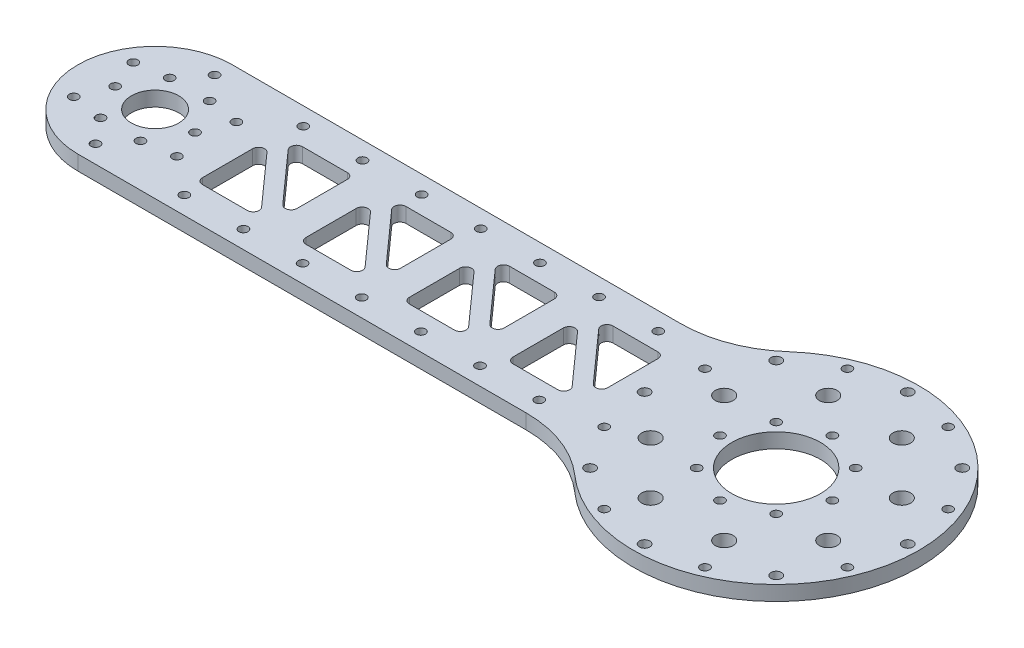
SolidWorks part; units mm, degrees
material "Thornel Mat VMA"
ref_plane "前视基准面" through (0, 0, 0) normal (0, 0, 1) x (1, 0, 0)
ref_plane "上视基准面" through (0, 0, 0) normal (0, 1, 0) x (1, 0, 0)
ref_plane "右视基准面" through (0, 0, 0) normal (1, 0, 0) x (0, 0, -1)
other "Configuration Table"
sketch "草图1" plane through (0, 0, 0) normal (0, 1, 0) x (1, 0, 0)
  line L1 (-105, -26.125) -> (105, -26.125)
  line L2 (-105, -26.125) -> (-105, 26.125)
  line L3 (-105, 26.125) -> (105, 26.125)
  line L4 (105, -26.125) -> (105, 26.125)
  line L5 (-105, -26.125) -> (105, 26.125) construction
  line L6 (-105, 26.125) -> (105, -26.125) construction
  circle A0 centre (-105, 0) radius 26.125
  point P0 (0, 0)
  dimension "D1" = 52.25
  dimension "D2" = 210
extrude "凸台-拉伸1" add sketch "草图1" along normal blind 5 contours A0 L1 L4 L3 | L2 A0 | L2 A0
sketch "草图2" plane through (0, 5, 0) normal (0, 1, 0) x (1, 0, 0)
  circle A0 centre (-105, 0) radius 13.5 construction
  circle A1 centre (-91.5, 0) radius 1.525
  circle A2 centre (-98.25, -11.6913) radius 1.525
  circle A3 centre (-111.75, -11.6913) radius 1.525
  circle A4 centre (-118.5, 0) radius 1.525
  circle A5 centre (-111.75, 11.6913) radius 1.525
  circle A6 centre (-98.25, 11.6913) radius 1.525
  point P17 (-105, 0)
  dimension "D1" = 27
  dimension "D2" = 3.05
  dimension "D3" = 6
extrude "切除-拉伸1" cut sketch "草图2" against normal through all
sketch "草图3" plane through (0, 5, 0) normal (0, 1, 0) x (1, 0, 0)
  line L0 (105, -26.125) -> (105, 26.125) construction
  circle A0 centre (105, 0) radius 48.25
  dimension "D1" = 96.5
extrude "凸台-拉伸2" add sketch "草图3" against normal up to surface (5 mm away) up to face at (-91.5, 0, 1.525)
sketch "草图4" plane through (0, 5, 0) normal (0, 1, 0) x (1, 0, 0)
  line L0 (-105, 26.125) -> (64.4347, 26.125) construction
  line L1 (-47, 26.125) -> (-147, 26.125)
  line L2 (-47, 26.125) -> (-47, -73.875)
  line L3 (-47, -73.875) -> (-147, -73.875)
  line L4 (-147, 26.125) -> (-147, -73.875)
  arc A0 (-105, 26.125) -> (-105, -26.125) centre (-105, 0) ccw construction
  dimension "D1" = 58
  dimension "D2" = 100
  dimension "D3" = 100
sketch "草图6" plane through (0, 5, 0) normal (0, 1, 0) x (1, 0, 0)
  line L0 (118.435, 13.435) -> (105, 0) construction
  line L1 (105, 0) -> (124, 0) construction
  circle A0 centre (105, 0) radius 19 construction
  circle A1 centre (118.435, 13.435) radius 1.525
  circle A2 centre (124, 0) radius 1.525
  circle A3 centre (118.435, -13.435) radius 1.525
  circle A4 centre (105, -19) radius 1.525
  circle A5 centre (91.565, -13.435) radius 1.525
  circle A6 centre (86, 0) radius 1.525
  circle A7 centre (91.565, 13.435) radius 1.525
  circle A8 centre (105, 19) radius 1.525
  point P22 (105, 0)
  dimension "D1" = 38
  dimension "D3" = 3.05
  dimension "D2" = 45
  dimension "D4" = 8
extrude "切除-拉伸4" cut sketch "草图6" against normal through all
sketch "草图7" plane through (0, 5, 0) normal (0, 1, 0) x (1, 0, 0)
  circle A0 centre (105, 0) radius 44.5 construction
  circle A1 centre (149.5, 0) radius 1.775
  circle A3 centre (136.4663, -31.4663) radius 1.775
  circle A4 centre (105, -44.5) radius 1.775
  circle A5 centre (73.5337, -31.4663) radius 1.775
  circle A6 centre (60.5, 0) radius 1.775
  circle A7 centre (73.5337, 31.4663) radius 1.775
  circle A8 centre (105, 44.5) radius 1.775
  circle A9 centre (136.4663, 31.4663) radius 1.775
  point P25 (105, 0)
  dimension "D1" = 89
  dimension "D2" = 3.55
  dimension "D3" = 8
extrude "切除-拉伸5" cut sketch "草图7" against normal through all
fillet "圆角1" radius 40 2 edges at (64.4347, 2.5, 26.125) (64.4347, 2.5, -26.125)
sketch "草图9" plane through (0, 5, 0) normal (0, 1, 0) x (1, 0, 0)
  circle A0 centre (105, 0) radius 14
  dimension "D1" = 28
extrude "切除-拉伸7" cut sketch "草图9" against normal through all
sketch "草图10" plane through (0, 5, 0) normal (0, 1, 0) x (1, 0, 0)
  circle A0 centre (-105, 0) radius 8
  dimension "D1" = 16
extrude "切除-拉伸8" cut sketch "草图10" against normal through all
sketch "草图11" plane through (0, 5, 0) normal (0, 1, 0) x (1, 0, 0)
  circle A0 centre (105, 0) radius 15
  dimension "D1" = 30
extrude "切除-拉伸9" cut sketch "草图11" against normal through all
sketch "草图12" plane through (0, 5, 0) normal (0, 1, 0) x (1, 0, 0)
  line L0 (105, 44.5) -> (105, 0) construction
  line L1 (117.4372, 30.0261) -> (105, 0) construction
  circle A0 centre (105, 0) radius 32.5 construction
  circle A1 centre (117.4372, 30.0261) radius 3
  circle A2 centre (135.0261, 12.4372) radius 3
  circle A3 centre (135.0261, -12.4372) radius 3
  circle A4 centre (117.4372, -30.0261) radius 3
  circle A5 centre (92.5628, -30.0261) radius 3
  circle A6 centre (74.9739, -12.4372) radius 3
  circle A7 centre (74.9739, 12.4372) radius 3
  circle A8 centre (92.5628, 30.0261) radius 3
  point P23 (105, 0)
  dimension "D1" = 65
  dimension "D3" = 6
  dimension "D2" = 22.5
  dimension "D4" = 8
extrude "切除-拉伸10" cut sketch "草图12" against normal through all
sketch "草图13" plane through (0, 5, 0) normal (0, 1, 0) x (1, 0, 0)
  line L0 (105, 44.5) -> (105, 0) construction
  line L1 (105, 0) -> (122.0294, 41.1126) construction
  circle A0 centre (105, 0) radius 44.5 construction
  circle A1 centre (122.0294, 41.1126) radius 1.525
  circle A2 centre (146.1126, 17.0294) radius 1.525
  circle A3 centre (146.1126, -17.0294) radius 1.525
  circle A4 centre (122.0294, -41.1126) radius 1.525
  circle A5 centre (87.9706, -41.1126) radius 1.525
  circle A6 centre (63.8874, -17.0294) radius 1.525
  circle A7 centre (63.8874, 17.0294) radius 1.525
  circle A8 centre (87.9706, 41.1126) radius 1.525
  point P23 (105, 0)
  dimension "D3" = 3.05
  dimension "D1" = 22.5
  dimension "D2" = 8
extrude "切除-拉伸11" cut sketch "草图13" against normal through all
sketch "草图17" plane through (0, 5, 0) normal (0, 1, 0) x (1, 0, 0)
  line L0 (42.5772, 9.8934) -> (35.238, 9.8934)
  line L1 (34.4811, 5.5801) -> (37.0911, 5.5801)
  line L2 (37.0911, 5.5801) -> (37.483, 7.8132)
  line L3 (37.483, 7.8132) -> (41.4928, 7.8132)
  line L4 (42.9809, 5.5801) -> (46.4742, 5.5801)
  line L5 (46.4742, 5.5801) -> (45.2007, 7.2203)
  line L6 (43.0953, 14.0169) -> (35.9608, 14.0169)
  line L7 (35.5775, 11.8231) -> (42.918, 11.8231)
  line L8 (24.225, 7.75) -> (22.1556, 5.5801)
  line L9 (22.1556, 5.5801) -> (31.8976, 5.5801)
  line L10 (31.8976, 5.5801) -> (33.9655, 7.75)
  line L11 (33.9655, 7.75) -> (24.225, 7.75)
  line L12 (24.5586, 10.8141) -> (22.7426, 8.8975)
  line L13 (22.7426, 8.8975) -> (32.7609, 8.8975)
  line L14 (32.7609, 8.8975) -> (34.5779, 10.8141)
  line L15 (34.5779, 10.8141) -> (24.5586, 10.8141)
  line L16 (33.0098, 11.8231) -> (35.0913, 14.0169)
  line L17 (35.0913, 14.0169) -> (25.337, 14.0169)
  line L18 (25.337, 14.0169) -> (23.2557, 11.8231)
  line L19 (23.2557, 11.8231) -> (33.0098, 11.8231)
  line L20 (24.2867, 14.0169) -> (14.7023, 14.0169)
  line L21 (14.7023, 14.0169) -> (12.609, 11.8231)
  line L22 (12.609, 11.8231) -> (16.569, 11.8231)
  line L23 (16.569, 11.8231) -> (15.4718, 5.5801)
  line L24 (15.4718, 5.5801) -> (18.083, 5.5801)
  line L25 (18.083, 5.5801) -> (19.1925, 11.8231)
  line L26 (19.1925, 11.8231) -> (22.1934, 11.8231)
  line L27 (22.1934, 11.8231) -> (24.2867, 14.0169)
  line L28 (10.0862, 10.6502) -> (5.4953, 10.6502)
  line L29 (5.698, 11.8234) -> (11.5491, 11.8234)
  line L30 (13.6181, 14.0169) -> (6.2899, 14.0169)
  line L31 (4.9411, 8.9726) -> (9.5442, 8.9726)
  line L32 (9.3293, 7.75) -> (2.9362, 7.75)
  line L33 (0.8806, 5.5803) -> (8.7374, 5.5803)
  line L34 (-7.2775, 13.2107) -> (-14.0368, 5.5801)
  line L35 (-14.0368, 5.5801) -> (-10.9478, 5.5801)
  line L36 (-9.8123, 5.5801) -> (0, 5.5801)
  line L37 (-4.3302, 14.0169) -> (-7.6269, 14.0169)
  line L38 (-7.2056, 13.2909) -> (-7.2594, 13.2302)
  line L39 (-24.2699, 14.0172) -> (-27.6879, 14.0172)
  line L40 (-27.6879, 14.0172) -> (-27.0207, 12.8684)
  line L41 (-30.4423, 5.5803) -> (-27.882, 5.5803)
  line L42 (-23.7812, 5.5803) -> (-21.6294, 5.5803)
  line L43 (-17.5155, 5.5803) -> (-14.9174, 5.5803)
  line L44 (-15.8647, 14.0172) -> (-19.217, 14.0172)
  line L45 (-18.6942, 13.1171) -> (-20.3655, 10.8649)
  line L46 (-33.6214, 14.0547) -> (-36.0703, 14.0547)
  line L47 (-36.9409, 5.5717) -> (-34.492, 5.5717)
  line L48 (-29.7231, 9.7455) -> (-29.7086, 9.8798)
  line L49 (-44.5301, 14.0172) -> (-51.9143, 14.0172)
  line L50 (-51.9143, 14.0172) -> (-52.2851, 11.8234)
  line L51 (-52.2851, 11.8234) -> (-44.8201, 11.8234)
  line L52 (-45.0088, 10.713) -> (-52.4744, 10.713)
  line L53 (-53.383, 5.5803) -> (-45.9674, 5.5803)
  line L54 (-57.4386, 14.0547) -> (-59.8876, 14.0547)
  line L55 (-60.7588, 5.5717) -> (-58.3098, 5.5717)
  line L56 (-69.6939, 9.8934) -> (-77.0331, 9.8934)
  line L57 (-77.7897, 5.5801) -> (-75.1798, 5.5801)
  line L58 (-74.7881, 7.8132) -> (-70.7782, 7.8132)
  line L59 (-69.2899, 5.5801) -> (-65.7969, 5.5801)
  line L60 (-65.7969, 5.5801) -> (-67.0704, 7.2203)
  line L61 (-69.1761, 14.0169) -> (-76.3187, 14.0169)
  line L62 (-76.6923, 11.8231) -> (-69.3529, 11.8231)
  arc A0 (-7.6269, 14.0169) -> (-7.2056, 13.2909) centre (943.6872, 565.5527) ccw
  circle A1 centre (149.5, 0) radius 1.775 construction
  spline S0 degree 3 poles (35.238, 9.8934) (34.9856, 8.4557) (34.7335, 7.018) (34.4811, 5.5801) knots 0 0 0 0 1 1 1 1
  spline S1 degree 3 poles (41.4928, 7.8132) (41.989, 7.0689) (42.4848, 6.3246) (42.9809, 5.5801) knots 0 0 0 0 1 1 1 1
  spline S2 degree 3 poles (45.2007, 7.2203) (44.7297, 7.8093) (44.4647, 8.1117) (44.229, 8.3295) knots 0 0 0 0 1 1 1 1
  spline S3 degree 3 poles (44.229, 8.3295) (44.633, 8.4051) (45.3798, 8.6843) (46.2546, 9.3994) (46.7238, 10.191) (46.9215, 10.8971) (46.9746, 11.5258) (46.8961, 12.175) (46.6232, 12.7245) (46.2118, 13.1646) (45.5315, 13.6262) (44.4526, 13.9541) (43.5316, 14.0169) (43.0953, 14.0169) knots 0 0 0 0 0.107095 0.214231 0.320875 0.374482 0.428088 0.499529 0.57097 0.642559 0.714147 0.857142 1 1 1 1
  spline S4 degree 3 poles (35.9608, 14.0169) (35.8331, 13.2857) (35.7052, 12.5545) (35.5775, 11.8231) knots 0 0 0 0 1 1 1 1
  spline S5 degree 3 poles (42.918, 11.8231) (43.322, 11.8231) (43.8028, 11.7177) (44.1482, 11.3761) (44.2415, 10.9675) (44.1099, 10.5076) (43.7446, 10.1631) (43.2199, 9.947) (42.7955, 9.8934) (42.5772, 9.8934) knots 0 0 0 0 0.226365 0.339877 0.453389 0.590814 0.726932 0.863344 1 1 1 1
  spline S6 degree 3 poles (5.4953, 10.6502) (4.9582, 10.6502) (4.6887, 10.8104) (4.6887, 11.1295) knots 0 0 0 0 1 1 1 1
  spline S7 degree 3 poles (4.6887, 11.1295) (4.6887, 11.6355) (4.9946, 11.8234) (5.698, 11.8234) knots 0 0 0 0 1 1 1 1
  spline S8 degree 3 poles (11.5491, 11.8234) (12.2388, 12.5546) (12.9286, 13.2858) (13.6181, 14.0169) knots 0 0 0 0 1 1 1 1
  spline S9 degree 3 poles (6.2899, 14.0169) (5.5501, 14.0169) (4.2968, 13.8593) (3.0258, 13.2071) (2.4268, 12.3951) (2.2063, 11.6339) (2.1323, 10.9062) (2.2775, 10.1413) (2.9399, 9.2707) (3.983, 8.9726) (4.9411, 8.9726) knots 0 0 0 0 0.145615 0.29142 0.437331 0.51021 0.583088 0.687231 0.791373 1 1 1 1
  spline S10 degree 3 poles (9.5442, 8.9726) (10.0741, 8.9726) (10.3386, 8.8052) (10.3386, 8.4681) knots 0 0 0 0 1 1 1 1
  spline S11 degree 3 poles (10.3386, 8.4681) (10.3386, 7.9793) (10.0332, 7.75) (9.3293, 7.75) knots 0 0 0 0 1 1 1 1
  spline S12 degree 3 poles (2.9362, 7.75) (2.2509, 7.0267) (1.5659, 6.3034) (0.8806, 5.5803) knots 0 0 0 0 1 1 1 1
  spline S13 degree 3 poles (8.7374, 5.5803) (9.4846, 5.5803) (10.7519, 5.7444) (12.0273, 6.4105) (12.7421, 7.4309) (12.8855, 8.279) (12.8855, 8.7338) knots 0 0 0 0 0.249902 0.499752 0.749752 1 1 1 1
  spline S14 degree 3 poles (12.8855, 8.7338) (12.8855, 9.9953) (11.9192, 10.6501) (10.0862, 10.6502) knots 0 0 0 0 1 1 1 1
  spline S15 degree 3 poles (-7.2594, 13.2302) (-7.2654, 13.223) (-7.2715, 13.2168) (-7.2775, 13.2107) knots 0 0 0 0 1 1 1 1
  spline S16 degree 3 poles (-10.9478, 5.5801) (-9.2999, 7.4467) (-7.6518, 9.3134) (-6.004, 11.1803) knots 0 0 0 0 1 1 1 1
  spline S17 degree 3 poles (-6.004, 11.1803) (-5.8168, 10.8083) (-5.4418, 10.0624) (-5.0188, 9.2241) (-4.727, 8.6411) (-4.4941, 8.1781) (-4.3302, 7.8764) (-4.2383, 7.7245) knots 0 0 0 0 0.324267 0.648534 0.736587 0.82464 1 1 1 1
  spline S18 degree 3 poles (-4.2383, 7.7245) (-4.4393, 7.7418) (-4.9243, 7.7536) (-6.1879, 7.7471) (-7.1429, 7.75) (-7.8452, 7.75) knots 0 0 0 0 0.217895 0.431995 1 1 1 1
  spline S19 degree 3 poles (-7.8452, 7.75) (-8.5008, 7.0267) (-9.1565, 6.3034) (-9.8123, 5.5801) knots 0 0 0 0 1 1 1 1
  spline S20 degree 3 poles (0, 5.5801) (-1.4455, 8.3913) (-2.8914, 11.2025) (-4.3302, 14.0169) knots 0 0 0 0 1 1 1 1
  spline S21 degree 3 poles (-27.0207, 12.8684) (-28.1613, 10.4389) (-29.3019, 8.0098) (-30.4423, 5.5803) knots 0 0 0 0 1 1 1 1
  spline S22 degree 3 poles (-27.882, 5.5803) (-27.6635, 6.0701) (-27.2302, 7.046) (-26.5756, 8.4925) (-26.0119, 9.8277) (-25.7133, 10.5288) (-25.5871, 10.8395) knots 0 0 0 0 0.260432 0.520865 0.760359 1 1 1 1
  spline S23 degree 3 poles (-25.5871, 10.8395) (-25.5447, 10.696) (-25.4575, 10.4083) (-25.3055, 9.9167) (-25.1006, 9.3185) (-24.8049, 8.4859) (-24.4556, 7.4982) (-24.1078, 6.5273) (-23.8864, 5.8831) (-23.7812, 5.5803) knots 0 0 0 0 0.134358 0.268072 0.402881 0.537952 0.697706 0.857461 1 1 1 1
  spline S24 degree 3 poles (-21.6294, 5.5803) (-21.4395, 5.8497) (-21.2526, 6.1306) (-21.0594, 6.3881) knots 0 0 0 0 1 1 1 1
  spline S25 degree 3 poles (-21.0594, 6.3881) (-20.8091, 6.7412) (-20.312, 7.4446) (-19.7024, 8.2987) (-19.2766, 8.9098) (-18.9507, 9.3699) (-18.5925, 9.8774) (-18.2449, 10.3882) (-18.0489, 10.6876) (-17.9571, 10.8395) knots 0 0 0 0 0.195984 0.391968 0.468306 0.544643 0.697057 0.849274 1 1 1 1
  spline S26 degree 3 poles (-17.9571, 10.8395) (-17.9398, 10.1506) (-17.8899, 9.477) (-17.8054, 8.5192) knots 0 0 0 0 1 1 1 1
  spline S27 degree 3 poles (-17.8054, 8.5192) (-17.7086, 7.5396) (-17.6121, 6.5599) (-17.5155, 5.5803) knots 0 0 0 0 1 1 1 1
  spline S28 degree 3 poles (-14.9174, 5.5803) (-15.2333, 8.3926) (-15.549, 11.2043) (-15.8647, 14.0172) knots 0 0 0 0 1 1 1 1
  spline S29 degree 3 poles (-19.217, 14.0172) (-19.0426, 13.7171) (-18.8685, 13.4171) (-18.6942, 13.1171) knots 0 0 0 0 1 1 1 1
  spline S30 degree 3 poles (-20.3655, 10.8649) (-20.6095, 10.5375) (-21.0294, 9.9748) (-21.499, 9.3231) (-21.8642, 8.8036) (-22.0637, 8.5069) (-22.1559, 8.3555) knots 0 0 0 0 0.250048 0.500501 0.750915 1 1 1 1
  spline S31 degree 3 poles (-22.1559, 8.3555) (-22.2492, 8.6402) (-22.43, 9.1558) (-22.7661, 10.0467) (-23.0245, 10.7478) (-23.5511, 12.091) (-23.9361, 13.1348) (-24.2699, 14.0172) knots 0 0 0 0 0.263018 0.39437 0.525721 0.600517 1 1 1 1
  spline S32 degree 3 poles (-36.0703, 14.0547) (-38.4668, 14.0547) (-40.6029, 12.1859) (-40.8392, 9.8798) knots 0 0 0 0 1 1 1 1
  spline S33 degree 3 poles (-40.8392, 9.8798) (-40.8434, 9.8352) (-40.8483, 9.7903) (-40.8525, 9.7455) knots 0 0 0 0 1 1 1 1
  spline S34 degree 3 poles (-40.8525, 9.7455) (-41.09, 7.4411) (-39.3392, 5.5717) (-36.9409, 5.5717) knots 0 0 0 0 1 1 1 1
  spline S35 degree 3 poles (-34.492, 5.5717) (-32.0955, 5.5717) (-29.9594, 7.4411) (-29.7231, 9.7455) knots 0 0 0 0 1 1 1 1
  spline S36 degree 3 poles (-29.7086, 9.8798) (-29.4723, 12.1859) (-31.2231, 14.0547) (-33.6214, 14.0547) knots 0 0 0 0 1 1 1 1
  spline S37 degree 3 poles (-42.0824, 10.6127) (-41.8001, 10.9652) (-41.6031, 11.4287) (-41.6031, 12.0379) knots 0 0 0 0 1 1 1 1
  spline S38 degree 3 poles (-41.6031, 12.0379) (-41.6031, 13.3488) (-42.6947, 14.0172) (-44.5301, 14.0172) knots 0 0 0 0 1 1 1 1
  spline S39 degree 3 poles (-44.8201, 11.8234) (-44.7357, 11.8234) (-44.5784, 11.8069) (-44.3621, 11.7379) (-44.2061, 11.612) (-44.1569, 11.3439) (-44.2177, 11.0358) (-44.4144, 10.8439) (-44.696, 10.7383) (-44.9, 10.713) (-45.0088, 10.713) knots 0 0 0 0 0.100056 0.200112 0.300214 0.400316 0.549976 0.699637 0.849818 1 1 1 1
  spline S40 degree 3 poles (-52.4744, 10.713) (-52.7771, 9.0023) (-53.0803, 7.2912) (-53.383, 5.5803) knots 0 0 0 0 1 1 1 1
  spline S41 degree 3 poles (-45.9674, 5.5803) (-45.1595, 5.5803) (-43.8729, 5.7604) (-42.7075, 6.4284) (-42.234, 7.1922) (-42.0862, 7.8648) (-42.0402, 8.4199) (-42.1048, 8.9622) (-42.4144, 9.557) (-42.8016, 9.8266) (-43.1049, 9.9187) knots 0 0 0 0 0.156782 0.313482 0.470492 0.548893 0.627294 0.720488 0.813681 1 1 1 1
  spline S42 degree 3 poles (-43.1049, 9.9187) (-42.7327, 10.0378) (-42.3687, 10.2616) (-42.0824, 10.6127) knots 0 0 0 0 1 1 1 1
  spline S43 degree 3 poles (-59.8876, 14.0547) (-62.2841, 14.0547) (-64.4201, 12.1859) (-64.6571, 9.8798) knots 0 0 0 0 1 1 1 1
  spline S44 degree 3 poles (-64.6571, 9.8798) (-64.6613, 9.8352) (-64.6655, 9.7903) (-64.6703, 9.7455) knots 0 0 0 0 1 1 1 1
  spline S45 degree 3 poles (-64.6703, 9.7455) (-64.9079, 7.4411) (-63.1565, 5.5717) (-60.7588, 5.5717) knots 0 0 0 0 1 1 1 1
  spline S46 degree 3 poles (-58.3098, 5.5717) (-55.9127, 5.5717) (-53.7773, 7.4411) (-53.5403, 9.7455) knots 0 0 0 0 1 1 1 1
  spline S47 degree 3 poles (-53.5403, 9.7455) (-53.5361, 9.7903) (-53.5307, 9.8352) (-53.5265, 9.8798) knots 0 0 0 0 1 1 1 1
  spline S48 degree 3 poles (-53.5265, 9.8798) (-53.2895, 12.1859) (-55.0409, 14.0547) (-57.4386, 14.0547) knots 0 0 0 0 1 1 1 1
  spline S49 degree 3 poles (-77.0331, 9.8934) (-77.2852, 8.4557) (-77.5376, 7.018) (-77.7897, 5.5801) knots 0 0 0 0 1 1 1 1
  spline S50 degree 3 poles (-75.1798, 5.5801) (-75.0491, 6.3246) (-74.9185, 7.0689) (-74.7881, 7.8132) knots 0 0 0 0 1 1 1 1
  spline S51 degree 3 poles (-70.7782, 7.8132) (-70.2821, 7.0689) (-69.786, 6.3246) (-69.2899, 5.5801) knots 0 0 0 0 1 1 1 1
  spline S52 degree 3 poles (-67.0704, 7.2203) (-67.541, 7.8095) (-67.8053, 8.1117) (-68.0408, 8.3295) knots 0 0 0 0 1 1 1 1
  spline S53 degree 3 poles (-68.0408, 8.3295) (-67.6378, 8.4051) (-66.8918, 8.6825) (-66.0163, 9.4005) (-65.5472, 10.191) (-65.3489, 10.8972) (-65.295, 11.5258) (-65.3743, 12.175) (-65.6479, 12.7243) (-66.0591, 13.1646) (-66.7401, 13.6276) (-67.8186, 13.9538) (-68.7395, 14.0169) (-69.1761, 14.0169) knots 0 0 0 0 0.107236 0.21404 0.320541 0.374076 0.427611 0.498956 0.570301 0.641742 0.713184 0.856623 1 1 1 1
  spline S54 degree 3 poles (-76.3187, 14.0169) (-76.4431, 13.2857) (-76.5678, 12.5545) (-76.6923, 11.8231) knots 0 0 0 0 1 1 1 1
  spline S55 degree 3 poles (-69.3529, 11.8231) (-68.9491, 11.8231) (-68.4683, 11.7178) (-68.1228, 11.3761) (-68.0294, 10.9676) (-68.1603, 10.5057) (-68.5267, 10.162) (-69.0516, 9.9473) (-69.4744, 9.8934) (-69.6939, 9.8934) knots 0 0 0 0 0.225137 0.338033 0.450929 0.587609 0.724081 0.861997 1 1 1 1
  dimension "D1" = 1099.6318
  dimension "D5" = 105.271
  dimension "D6" = 106.4047
  dimension "D7" = 106.5191
  dimension "D8" = 106.582
  dimension "D13" = 113.5392
  dimension "D14" = 113.9225
  dimension "D15" = 794.1872
  dimension "D16" = 114.4087
  dimension "D17" = 114.9221
  dimension "D18" = 103.0258
  dimension "D19" = 115.5345
  dimension "D20" = 116.4902
  dimension "D21" = 116.7391
  dimension "D22" = 117.6024
  dimension "D23" = 124.163
  dimension "D24" = 124.9414
  dimension "D25" = 104.2993
  dimension "D26" = 125.275
  dimension "D27" = 126.2443
  dimension "D28" = 126.7574
  dimension "D29" = 106.9228
  dimension "D30" = 127.3444
  dimension "D31" = 130.3075
  dimension "D32" = 131.417
  dimension "D33" = 132.931
  dimension "D34" = 134.0282
  dimension "D35" = 108.0072
  dimension "D36" = 135.8819
  dimension "D37" = 136.6145
  dimension "D38" = 112.017
  dimension "D39" = 137.9509
  dimension "D40" = 139.1614
  dimension "D41" = 139.4138
  dimension "D42" = 139.9558
  dimension "D43" = 140.1707
  dimension "D44" = 140.7626
  dimension "D45" = 143.2101
  dimension "D46" = 143.802
  dimension "D47" = 144.0047
  dimension "D48" = 144.5589
  dimension "D49" = 144.8113
  dimension "D50" = 146.5638
  dimension "D51" = 148.6194
  dimension "D52" = 149.5
  dimension "D53" = 153.7383
  dimension "D54" = 153.8302
  dimension "D55" = 155.504
  dimension "D56" = 156.7056
  dimension "D57" = 156.7594
  dimension "D58" = 156.7775
  dimension "D59" = 157.1269
  dimension "D60" = 157.3452
  dimension "D61" = 159.3123
  dimension "D62" = 160.4478
  dimension "D63" = 163.5368
  dimension "D64" = 164.4174
  dimension "D65" = 165.3647
  dimension "D66" = 167.0155
  dimension "D67" = 167.3054
  dimension "D68" = 167.4571
  dimension "D69" = 168.1942
  dimension "D70" = 168.717
  dimension "D71" = 169.8655
  dimension "D72" = 170.5594
  dimension "D73" = 171.1294
  dimension "D74" = 171.6559
  dimension "D75" = 173.2812
  dimension "D76" = 173.7699
  dimension "D77" = 175.0871
  dimension "D78" = 176.5207
  dimension "D79" = 177.1879
  dimension "D80" = 177.382
  dimension "D81" = 179.2086
  dimension "D82" = 179.2231
  dimension "D83" = 179.9423
  dimension "D84" = 112.4089
  dimension "D85" = 114.262
  dimension "D86" = 115.0189
  dimension "D87" = 125.2133
  dimension "D88" = 190.3392
  dimension "D89" = 190.3525
  dimension "D90" = 191.1031
  dimension "D91" = 191.5824
  dimension "D92" = 192.6049
  dimension "D93" = 194.0301
  dimension "D94" = 194.3201
  dimension "D95" = 194.5088
  dimension "D96" = 195.4674
  dimension "D97" = 201.4143
  dimension "D98" = 201.7851
  dimension "D99" = 201.9744
  dimension "D100" = 202.883
  dimension "D101" = 203.0265
  dimension "D102" = 203.0403
  dimension "D103" = 127.3066
  dimension "D104" = 134.7977
  dimension "D105" = 183.1214
  dimension "D106" = 183.992
  dimension "D107" = 214.1571
  dimension "D108" = 214.1703
  dimension "D109" = 185.5703
  dimension "D110" = 206.9386
  dimension "D111" = 217.5408
  dimension "D112" = 218.6761
  dimension "D113" = 218.7899
  dimension "D114" = 218.8529
  dimension "D115" = 207.8098
  dimension "D116" = 216.5704
  dimension "D117" = 219.1939
  dimension "D118" = 220.2782
  dimension "D119" = 225.8187
  dimension "D120" = 226.1923
  dimension "D121" = 224.6798
  dimension "D122" = 5.5717
  dimension "D123" = 5.5801
  dimension "D124" = 5.5803
  dimension "D125" = 6.3881
  dimension "D126" = 7.2203
  dimension "D127" = 7.7245
  dimension "D128" = 7.75
  dimension "D129" = 7.8132
  dimension "D130" = 8.3295
  dimension "D131" = 8.3555
  dimension "D132" = 8.4681
  dimension "D133" = 8.5192
  dimension "D134" = 8.7338
  dimension "D135" = 8.8975
  dimension "D136" = 8.9726
  dimension "D137" = 9.7455
  dimension "D138" = 9.8798
  dimension "D139" = 9.8934
  dimension "D140" = 9.9187
  dimension "D141" = 10.6127
  dimension "D142" = 10.6502
  dimension "D143" = 10.713
  dimension "D144" = 10.8141
  dimension "D145" = 10.8395
  dimension "D146" = 10.8649
  dimension "D147" = 11.1295
  dimension "D148" = 11.1803
  dimension "D149" = 11.8231
  dimension "D150" = 11.8234
  dimension "D151" = 12.0379
  dimension "D152" = 12.8684
  dimension "D153" = 13.1171
  dimension "D154" = 13.2107
  dimension "D155" = 13.2302
  dimension "D156" = 13.2909
  dimension "D157" = 14.0172
  dimension "D158" = 14.0547
sketch "草图18" plane through (0, 5, 0) normal (0, 1, 0) x (1, 0, 0)
  line L0 (-40.1586, 20.125) -> (49959.8414, 20.125) construction
  line L1 (-105, 26.125) -> (46.5573, 26.125) construction
  circle A0 centre (45, 20.125) radius 1.525
  circle A1 centre (105, 0) radius 15 construction
  circle A2 centre (25, 20.125) radius 1.525
  circle A3 centre (5, 20.125) radius 1.525
  circle A4 centre (-15, 20.125) radius 1.525
  circle A5 centre (-35, 20.125) radius 1.525
  circle A6 centre (-55, 20.125) radius 1.525
  circle A7 centre (-75, 20.125) radius 1.525
  dimension "D2" = 3.05
  dimension "D1" = 6
  dimension "D3" = 60
  dimension "D5" = 20
  dimension "D4" = 7
extrude "切除-拉伸13" cut sketch "草图18" against normal through all
sketch "草图19" plane through (0, 5, 0) normal (0, 1, 0) x (1, 0, 0)
  line L0 (0, 0) -> (50000, 0) construction
  circle A0 centre (45, 20.125) radius 2.525
  circle A1 centre (5, 20.125) radius 2.525
  circle A2 centre (-35, 20.125) radius 2.525
  circle A3 centre (-75, 20.125) radius 2.525
  dimension "D1" = 5.05
  dimension "D3" = 40
  dimension "D2" = 4
mirror "镜向2" about plane through (0, 0, 0) normal (0, 0, 1) of "切除-拉伸13"
sketch "草图21" plane through (0, 5, 0) normal (0, 1, 0) x (1, 0, 0)
  line L0 (-75, 20.125) -> (-105, 20.125) construction
  circle A0 centre (-105, 0) radius 20.125 construction
  circle A1 centre (-105, 20.125) radius 1.525
  circle A2 centre (-87.5712, 10.0625) radius 1.525
  circle A3 centre (-87.5712, -10.0625) radius 1.525
  circle A4 centre (-105, -20.125) radius 1.525
  circle A5 centre (-122.4288, -10.0625) radius 1.525
  circle A6 centre (-122.4288, 10.0625) radius 1.525
  point P20 (-105, 0)
  dimension "D1" = 3.05
  dimension "D2" = 6
extrude "切除-拉伸15" cut sketch "草图21" against normal through all
sketch "草图22" plane through (0, 0, 0) normal (0, -1, 0) x (1, 0, 0)
  line L3 (-69.1816, -14) -> (-54, -14)
  line L4 (-55.4919, 6.3354) -> (-70.6735, -10.668)
  line L5 (-52, -12) -> (-52, 5.0034)
  line L6 (-69.1816, -14) -> (-54, -14)
  line L7 (-55.4919, 6.3354) -> (-70.6735, -10.668)
  line L8 (-52, -12) -> (-52, 5.0034)
  line L9 (-73.5081, -6.3354) -> (-58.3265, 10.668)
  line L10 (-77, 12) -> (-77, -5.0034)
  line L11 (-59.8184, 14) -> (-75, 14)
  line L12 (-73.5081, -6.3354) -> (-58.3265, 10.668)
  line L13 (-77, 12) -> (-77, -5.0034)
  line L14 (-59.8184, 14) -> (-75, 14)
  line L15 (-42, 12) -> (-42, -5.0034)
  line L16 (-24.8184, 14) -> (-40, 14)
  line L17 (-38.5081, -6.3354) -> (-23.3265, 10.668)
  line L18 (-42, 12) -> (-42, -5.0034)
  line L19 (-24.8184, 14) -> (-40, 14)
  line L20 (-38.5081, -6.3354) -> (-23.3265, 10.668)
  line L21 (-34.1816, -14) -> (-19, -14)
  line L22 (-20.4919, 6.3354) -> (-35.6735, -10.668)
  line L23 (-17, -12) -> (-17, 5.0034)
  line L24 (-34.1816, -14) -> (-19, -14)
  line L25 (-20.4919, 6.3354) -> (-35.6735, -10.668)
  line L26 (-17, -12) -> (-17, 5.0034)
  line L27 (-7, 12) -> (-7, -5.0034)
  line L28 (10.1816, 14) -> (-5, 14)
  line L29 (-3.5081, -6.3354) -> (11.6735, 10.668)
  line L30 (-7, 12) -> (-7, -5.0034)
  line L31 (10.1816, 14) -> (-5, 14)
  line L32 (-3.5081, -6.3354) -> (11.6735, 10.668)
  line L33 (0.8184, -14) -> (16, -14)
  line L34 (14.5081, 6.3354) -> (-0.6735, -10.668)
  line L35 (18, -12) -> (18, 5.0034)
  line L36 (0.8184, -14) -> (16, -14)
  line L37 (14.5081, 6.3354) -> (-0.6735, -10.668)
  line L38 (18, -12) -> (18, 5.0034)
  line L39 (28, 12) -> (28, -5.0034)
  line L40 (45.1816, 14) -> (30, 14)
  line L41 (31.4919, -6.3354) -> (46.6735, 10.668)
  line L42 (28, 12) -> (28, -5.0034)
  line L43 (45.1816, 14) -> (30, 14)
  line L44 (31.4919, -6.3354) -> (46.6735, 10.668)
  line L45 (35.8184, -14) -> (51, -14)
  line L46 (49.5081, 6.3354) -> (34.3265, -10.668)
  line L47 (53, -12) -> (53, 5.0034)
  line L48 (35.8184, -14) -> (51, -14)
  line L49 (49.5081, 6.3354) -> (34.3265, -10.668)
  line L50 (53, -12) -> (53, 5.0034)
  arc A3 (-70.6735, -10.668) -> (-69.1816, -14) centre (-69.1816, -12) ccw
  arc A4 (-52, 5.0034) -> (-55.4919, 6.3354) centre (-54, 5.0034) ccw
  arc A5 (-54, -14) -> (-52, -12) centre (-54, -12) ccw
  arc A6 (-70.6735, -10.668) -> (-69.1816, -14) centre (-69.1816, -12) ccw
  arc A7 (-52, 5.0034) -> (-55.4919, 6.3354) centre (-54, 5.0034) ccw
  arc A8 (-54, -14) -> (-52, -12) centre (-54, -12) ccw
  arc A9 (-77, -5.0034) -> (-73.5081, -6.3354) centre (-75, -5.0034) ccw
  arc A10 (-75, 14) -> (-77, 12) centre (-75, 12) ccw
  arc A11 (-58.3265, 10.668) -> (-59.8184, 14) centre (-59.8184, 12) ccw
  arc A12 (-77, -5.0034) -> (-73.5081, -6.3354) centre (-75, -5.0034) ccw
  arc A13 (-75, 14) -> (-77, 12) centre (-75, 12) ccw
  arc A14 (-58.3265, 10.668) -> (-59.8184, 14) centre (-59.8184, 12) ccw
  arc A15 (-42, -5.0034) -> (-38.5081, -6.3354) centre (-40, -5.0034) ccw
  arc A16 (-40, 14) -> (-42, 12) centre (-40, 12) ccw
  arc A17 (-23.3265, 10.668) -> (-24.8184, 14) centre (-24.8184, 12) ccw
  arc A18 (-42, -5.0034) -> (-38.5081, -6.3354) centre (-40, -5.0034) ccw
  arc A19 (-40, 14) -> (-42, 12) centre (-40, 12) ccw
  arc A20 (-23.3265, 10.668) -> (-24.8184, 14) centre (-24.8184, 12) ccw
  arc A21 (-35.6735, -10.668) -> (-34.1816, -14) centre (-34.1816, -12) ccw
  arc A22 (-17, 5.0034) -> (-20.4919, 6.3354) centre (-19, 5.0034) ccw
  arc A23 (-19, -14) -> (-17, -12) centre (-19, -12) ccw
  arc A24 (-35.6735, -10.668) -> (-34.1816, -14) centre (-34.1816, -12) ccw
  arc A25 (-17, 5.0034) -> (-20.4919, 6.3354) centre (-19, 5.0034) ccw
  arc A26 (-19, -14) -> (-17, -12) centre (-19, -12) ccw
  arc A27 (-5, 14) -> (-7, 12) centre (-5, 12) ccw
  arc A28 (11.6735, 10.668) -> (10.1816, 14) centre (10.1816, 12) ccw
  arc A29 (-7, -5.0034) -> (-3.5081, -6.3354) centre (-5, -5.0034) ccw
  arc A30 (-5, 14) -> (-7, 12) centre (-5, 12) ccw
  arc A31 (11.6735, 10.668) -> (10.1816, 14) centre (10.1816, 12) ccw
  arc A32 (-7, -5.0034) -> (-3.5081, -6.3354) centre (-5, -5.0034) ccw
  arc A33 (-0.6735, -10.668) -> (0.8184, -14) centre (0.8184, -12) ccw
  arc A34 (18, 5.0034) -> (14.5081, 6.3354) centre (16, 5.0034) ccw
  arc A35 (16, -14) -> (18, -12) centre (16, -12) ccw
  arc A36 (-0.6735, -10.668) -> (0.8184, -14) centre (0.8184, -12) ccw
  arc A37 (18, 5.0034) -> (14.5081, 6.3354) centre (16, 5.0034) ccw
  arc A38 (16, -14) -> (18, -12) centre (16, -12) ccw
  arc A39 (30, 14) -> (28, 12) centre (30, 12) ccw
  arc A40 (46.6735, 10.668) -> (45.1816, 14) centre (45.1816, 12) ccw
  arc A41 (28, -5.0034) -> (31.4919, -6.3354) centre (30, -5.0034) ccw
  arc A42 (30, 14) -> (28, 12) centre (30, 12) ccw
  arc A43 (46.6735, 10.668) -> (45.1816, 14) centre (45.1816, 12) ccw
  arc A44 (28, -5.0034) -> (31.4919, -6.3354) centre (30, -5.0034) ccw
  arc A45 (34.3265, -10.668) -> (35.8184, -14) centre (35.8184, -12) ccw
  arc A46 (53, 5.0034) -> (49.5081, 6.3354) centre (51, 5.0034) ccw
  arc A47 (51, -14) -> (53, -12) centre (51, -12) ccw
  arc A48 (34.3265, -10.668) -> (35.8184, -14) centre (35.8184, -12) ccw
  arc A49 (53, 5.0034) -> (49.5081, 6.3354) centre (51, 5.0034) ccw
  arc A50 (51, -14) -> (53, -12) centre (51, -12) ccw
  dimension "D1" = 0
  dimension "D2" = 0
  dimension "D3" = 0
  dimension "D4" = 0
  dimension "D5" = 0
  dimension "D6" = 0
  dimension "D7" = 0
  dimension "D8" = 0
extrude "切除-拉伸16" cut sketch "草图22" against normal through all
